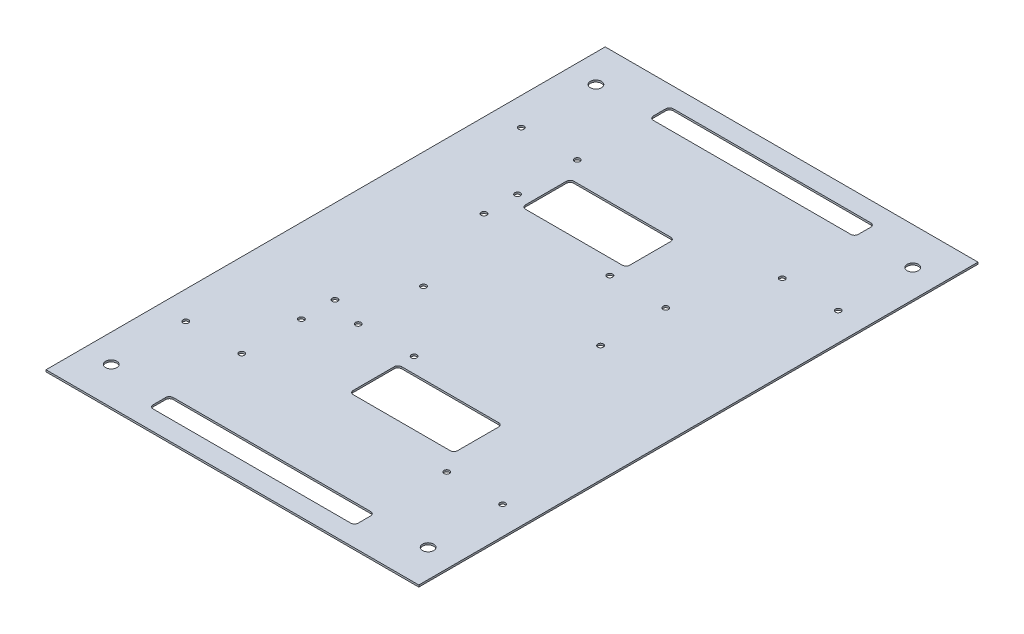
SolidWorks part; units mm, degrees
ref_plane "Plan de face" through (0, 0, 0) normal (0, 0, 1) x (1, 0, 0)
ref_plane "Plan de dessus" through (0, 0, 0) normal (0, 1, 0) x (1, 0, 0)
ref_plane "Plan de droite" through (0, 0, 0) normal (1, 0, 0) x (0, 0, -1)
sketch "Esquisse1" plane through (0, 0, 0) normal (0, 1, 0) x (1, 0, 0)
  line L0 (-2, -76.175) -> (42, -76.175) construction
  line L1 (-100, -150) -> (100, -150)
  line L2 (-100, -150) -> (-100, 150)
  line L3 (-100, 150) -> (100, 150)
  line L4 (100, -150) -> (100, 150)
  line L5 (-100, -150) -> (100, 150) construction
  line L6 (-100, 150) -> (100, -150) construction
  line L7 (-6, -53.175) -> (46, -53.175)
  line L8 (-8, -55.175) -> (-8, -77.175)
  line L9 (-6, -79.175) -> (46, -79.175)
  line L10 (48, -55.175) -> (48, -77.175)
  line L11 (47, -56.175) -> (-7, -56.175) construction
  line L12 (0, 0) -> (0, -150) construction
  line L13 (47, -150) -> (47, -53.175) construction
  line L14 (100, 0) -> (-100, 0) construction
  line L15 (-7, -53.175) -> (-7, -150) construction
  line L16 (0, 150) -> (0, 0) construction
  line L17 (7, 76.175) -> (-47, 76.175) construction
  line L18 (-46, 79.175) -> (6, 79.175)
  line L19 (-48, 77.175) -> (-48, 55.175)
  line L20 (-46, 53.175) -> (6, 53.175)
  line L21 (8, 77.175) -> (8, 55.175)
  line L22 (-47, 56.175) -> (7, 56.175) construction
  line L23 (-47, 56.175) -> (-47, 150) construction
  line L24 (-55, 0) -> (-55, 75.3308) construction
  line L25 (7, 56.175) -> (7, 150) construction
  line L26 (-53, -139.5001) -> (53, -139.5001)
  line L27 (55, -137.5001) -> (55, -130.7728)
  line L28 (53, -128.7728) -> (-53, -128.7728)
  line L29 (-57.5, -138.5001) -> (57.5, -138.5001) construction
  line L30 (57.5, -129.5001) -> (-57.5, -129.5001) construction
  line L31 (-55, -137.5001) -> (-55, -130.7728)
  line L32 (-55, 137.5001) -> (-55, 130.7728)
  line L33 (53, 128.7728) -> (-53, 128.7728)
  line L34 (55, 137.5001) -> (55, 130.7728)
  line L35 (-53, 139.5001) -> (53, 139.5001)
  arc A0 (46, -79.175) -> (48, -77.175) centre (46, -77.175) ccw
  arc A1 (48, -55.175) -> (46, -53.175) centre (46, -55.175) ccw
  arc A2 (-6, -53.175) -> (-8, -55.175) centre (-6, -55.175) ccw
  arc A3 (-8, -77.175) -> (-6, -79.175) centre (-6, -77.175) ccw
  arc A4 (8, 55.175) -> (6, 53.175) centre (6, 55.175) cw
  arc A5 (8, 77.175) -> (6, 79.175) centre (6, 77.175) ccw
  arc A6 (-46, 79.175) -> (-48, 77.175) centre (-46, 77.175) ccw
  arc A7 (-48, 55.175) -> (-46, 53.175) centre (-46, 55.175) ccw
  circle A8 centre (-37.5, -45) radius 1.5
  circle A9 centre (-7.5, -45) radius 1.5
  circle A10 centre (-37.5, -10) radius 1.5
  circle A11 centre (37.5, 10) radius 1.5
  circle A12 centre (37.5, 45) radius 1.5
  circle A13 centre (7.5, 45) radius 1.5
  circle A14 centre (85, 130) radius 3
  circle A15 centre (-85, 130) radius 3
  circle A16 centre (85, -130) radius 3
  circle A17 centre (-85, -130) radius 3
  circle A18 centre (-55, 40) radius 1.5
  circle A19 centre (-55, 58) radius 1.5
  circle A20 centre (-55, -58) radius 1.5
  circle A21 centre (-55, -40) radius 1.5
  arc A22 (53, -128.7728) -> (55, -130.7728) centre (53, -130.7728) cw
  arc A23 (53, -139.5001) -> (55, -137.5001) centre (53, -137.5001) ccw
  arc A24 (-55, -137.5001) -> (-53, -139.5001) centre (-53, -137.5001) ccw
  arc A25 (-55, -130.7728) -> (-53, -128.7728) centre (-53, -130.7728) cw
  arc A26 (-55, 130.7728) -> (-53, 128.7728) centre (-53, 130.7728) ccw
  arc A27 (-55, 137.5001) -> (-53, 139.5001) centre (-53, 137.5001) cw
  arc A28 (53, 128.7728) -> (55, 130.7728) centre (53, 130.7728) ccw
  arc A29 (53, 139.5001) -> (55, 137.5001) centre (53, 137.5001) cw
  circle A30 centre (-85, -90) radius 1.5
  circle A31 centre (-55, -90) radius 1.5
  circle A32 centre (85, -90) radius 1.5
  circle A33 centre (55, -90) radius 1.5
  circle A34 centre (55, 90) radius 1.5
  circle A35 centre (85, 90) radius 1.5
  circle A36 centre (-55, 90) radius 1.5
  circle A37 centre (-85, 90) radius 1.5
  point P0 (0, 0)
  point P93 (0, -139.5001)
  point P101 (0, -128.7728)
  point P107 (55, -128.7728)
  point P110 (55, -139.5001)
  point P113 (-55, -139.5001)
  point P116 (-55, -128.7728)
  point P119 (-55, 128.7728)
  point P122 (-55, 139.5001)
  point P125 (55, 128.7728)
  point P128 (55, 139.5001)
  dimension "D11" = 2
  dimension "D12" = 3
  dimension "D13" = 3
  dimension "D14" = 3
  dimension "D15" = 3
  dimension "D16" = 3
  dimension "D17" = 3
  dimension "D18" = 6
  dimension "D20" = 130
  dimension "D19" = 85
  dimension "D22" = 40
  dimension "D23" = 3
  dimension "D24" = 3
  dimension "D25" = 18
  dimension "D29" = 2
  dimension "D30" = 3
  dimension "D31" = 15
  dimension "D32" = 60
  dimension "D33" = 3
  dimension "D34" = 60
  dimension "D35" = 30
  dimension "D1" = 200
  dimension "D2" = 300
  dimension "D3" = 3
  dimension "D4" = 3
  dimension "D5" = 1
  dimension "D6" = 1
  dimension "D7" = 3
  dimension "D8" = 3
  dimension "D9" = 1
  dimension "D10" = 1
  dimension "D21" = 55
  dimension "D26" = 1
  dimension "D27" = 0.7272
  dimension "D28" = 55
extrude "Boss.-Extru.1" add sketch "Esquisse1" along normal blind 1
